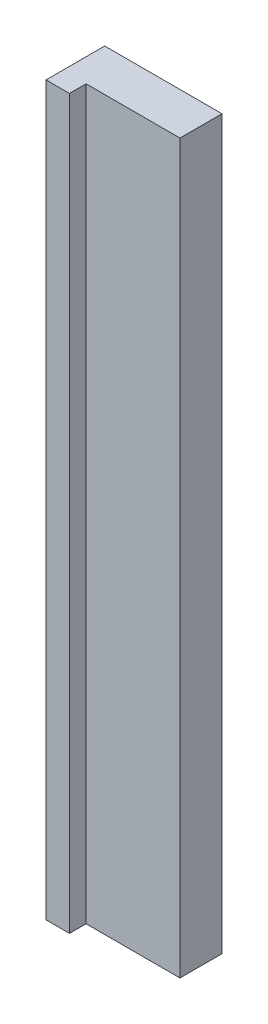
SolidWorks part; units mm, degrees
material "Chêne"
ref_plane "Plan de face" through (0, 0, 0) normal (0, 0, 1) x (1, 0, 0)
ref_plane "Plan de dessus" through (0, 0, 0) normal (0, 1, 0) x (1, 0, 0)
ref_plane "Plan de droite" through (0, 0, 0) normal (1, 0, 0) x (0, 0, -1)
sketch "Esquisse1" plane through (0, 0, 0) normal (0, 0, 1) x (1, 0, 0)
  line L0 (82, -211) -> (82, 141) construction
  line L1 (-23, 141) -> (37, 141)
  line L2 (-23, 141) -> (-23, -231)
  line L3 (-23, -231) -> (37, -231)
  line L4 (37, 141) -> (37, -231)
  line L6 (11, -231) -> (-11, -231) construction
  line L7 (-11, 141) -> (-11, -211) construction
  line L9 (82, 141) -> (-11, 141) construction
  dimension "D1" = 45
  dimension "D2" = 12
extrude "Boss.-Extru.1" add sketch "Esquisse1" along normal up to surface (21.5 mm away) contours L4 L3 L2 L1
sketch "Esquisse2" plane through (0, 0, 21.5) normal (0, 0, 1) x (1, 0, 0)
  line L1 (-23, 141) -> (-11, 141)
  line L2 (-23, 141) -> (-23, -231)
  line L3 (-23, -231) -> (-11, -231)
  line L4 (-11, 141) -> (-11, -231)
  line L5 (37, -231) -> (-23, -231) construction
  line L6 (-11, 141) -> (-11, -211) construction
extrude "Boss.-Extru.2" add sketch "Esquisse2" along normal up to surface (8.5 mm away)
